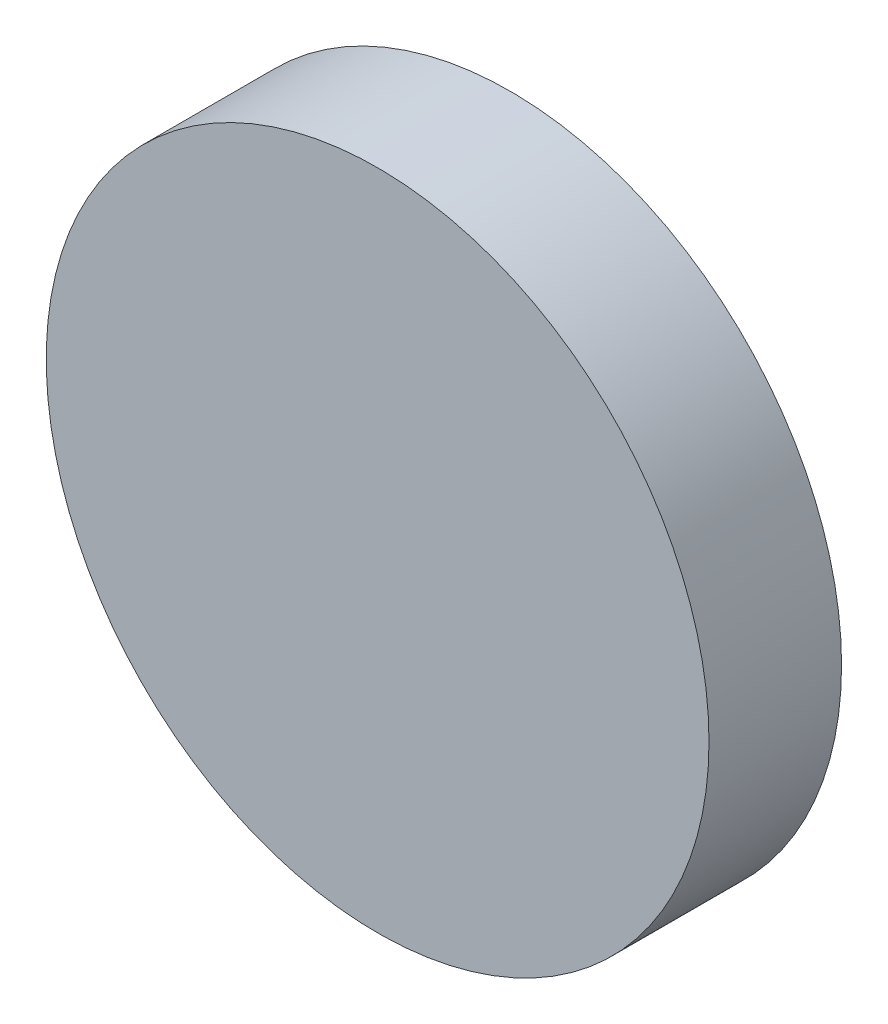
SolidWorks part; units mm, degrees
ref_plane "前视基准面" through (0, 0, 0) normal (0, 0, 1) x (1, 0, 0)
ref_plane "上视基准面" through (0, 0, 0) normal (0, 1, 0) x (1, 0, 0)
ref_plane "右视基准面" through (0, 0, 0) normal (1, 0, 0) x (0, 0, -1)
sketch "草图1" plane through (0, 0, 0) normal (0, 0, 1) x (1, 0, 0)
  circle A0 centre (0, 0) radius 25
  dimension "D1" = 50
extrude "凸台-拉伸1" add sketch "草图1" along normal blind 10
